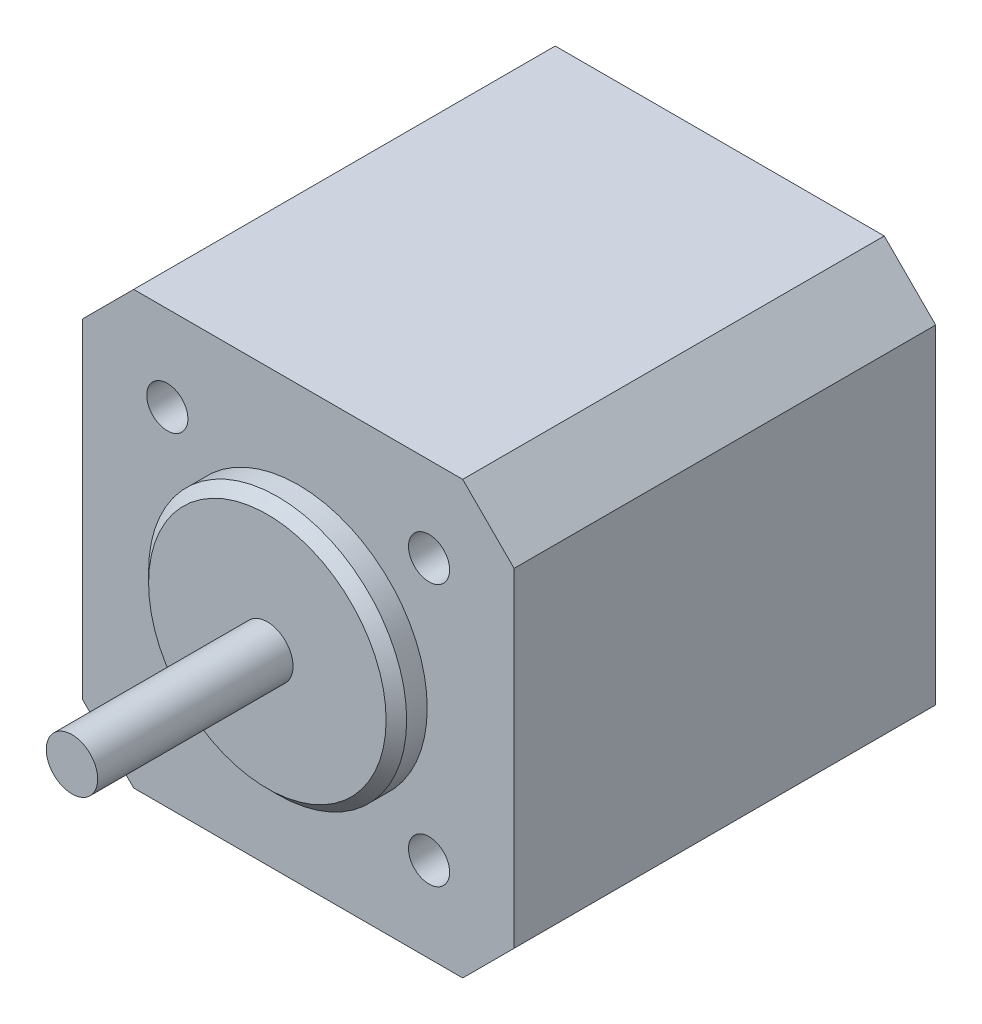
SolidWorks part; units mm, degrees
ref_plane "Alzado" through (0, 0, 0) normal (0, 0, 1) x (1, 0, 0)
ref_plane "Planta" through (0, 0, 0) normal (0, 1, 0) x (1, 0, 0)
ref_plane "Vista lateral" through (0, 0, 0) normal (1, 0, 0) x (0, 0, -1)
sketch "Croquis1" plane through (0, 0, 0) normal (0, 0, 1) x (1, 0, 0)
  line L0 (-21, 16) -> (-16, 21)
  line L1 (-16, -21) -> (16, -21)
  line L2 (-21, -16) -> (-21, 16)
  line L3 (-16, 21) -> (16, 21)
  line L4 (21, -16) -> (21, 16)
  line L5 (-21, -21) -> (21, 21) construction
  line L6 (-21, 21) -> (21, -21) construction
  line L7 (16, 21) -> (21, 16)
  line L8 (16, -21) -> (21, -16)
  line L9 (-16, -21) -> (-21, -16)
  circle A0 centre (0, 0) radius 18 construction
  circle A1 centre (12.7279, 12.7279) radius 2
  circle A2 centre (12.7279, -12.7279) radius 2
  circle A3 centre (-12.7279, -12.7279) radius 2
  circle A4 centre (-12.7279, 12.7279) radius 2
  point P0 (0, 0)
  point P8 (12.7279, 12.7279)
  point P20 (0, 0)
  dimension "D3" = 36
  dimension "D4" = 4
  dimension "D1" = 42
  dimension "D2" = 42
  dimension "D5" = 4
extrude "Saliente-Extruir1" add sketch "Croquis1" along normal blind 41
sketch "Croquis2" plane through (0, 0, 41) normal (0, 0, 1) x (1, 0, 0)
  circle A0 centre (0, 0) radius 12.55
  dimension "D1" = 25.1
extrude "Saliente-Extruir2" add sketch "Croquis2" along normal blind 3
sketch "Croquis3" plane through (0, 0, 44) normal (0, 0, 1) x (1, 0, 0)
  circle A0 centre (0, 0) radius 2.5
  dimension "D1" = 5
extrude "Saliente-Extruir3" add sketch "Croquis3" along normal blind 19
chamfer "Chaflán1" distance 1 angle 45 1 edges at (12.55, 0, 44)
